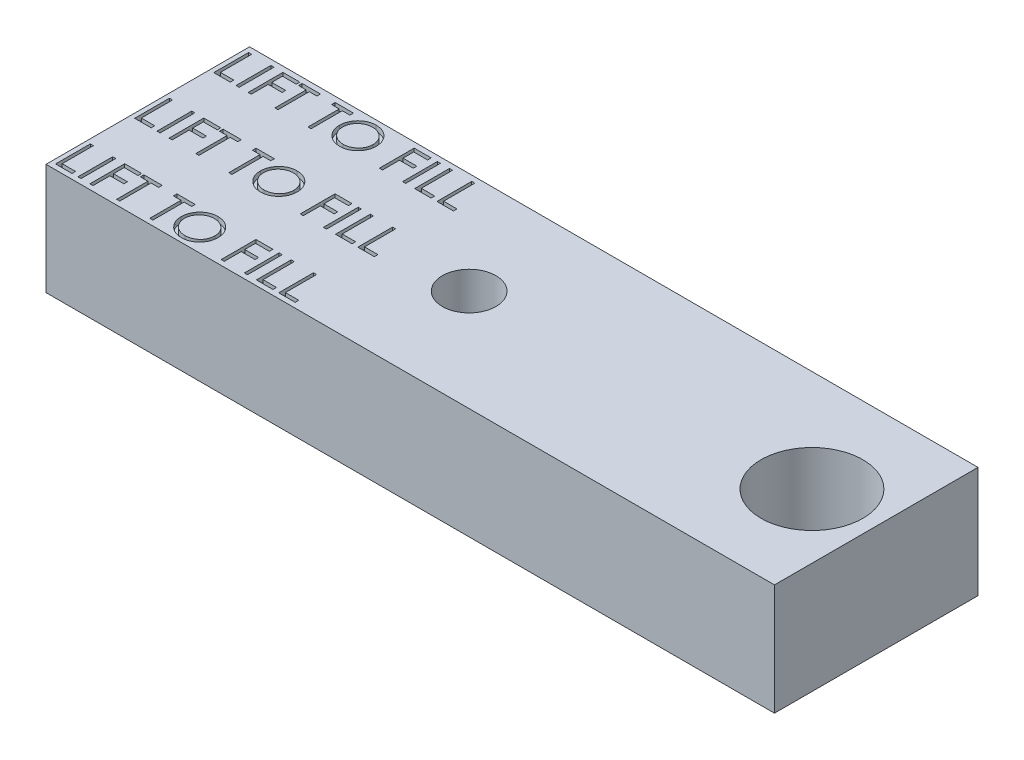
SolidWorks part; units mm, degrees
ref_plane "Front Plane" through (0, 0, 0) normal (0, 0, 1) x (1, 0, 0)
ref_plane "Top Plane" through (0, 0, 0) normal (0, 1, 0) x (1, 0, 0)
ref_plane "Right Plane" through (0, 0, 0) normal (1, 0, 0) x (0, 0, -1)
sketch "Sketch1" plane through (0, 0, 0) normal (0, 1, 0) x (1, 0, 0)
  line L1 (0, 0) -> (34.544, 0)
  line L2 (0, 0) -> (0, 9.652)
  line L3 (0, 9.652) -> (34.544, 9.652)
  line L4 (34.544, 0) -> (34.544, 9.652)
  dimension "D1" = 34.544
  dimension "D2" = 9.652
extrude "Boss-Extrude1" add sketch "Sketch1" along normal blind 5.2705
sketch "Sketch2" plane through (0, 5.2705, 0) normal (0, 1, 0) x (1, 0, 0)
  line L0 (34.544, 0) -> (34.544, 9.652) construction
  line L1 (0, 9.652) -> (0, 0) construction
  line L2 (34.544, 4.826) -> (0, 4.826) construction
  circle A0 centre (31.496, 4.826) radius 2.413
  circle A1 centre (15.24, 4.826) radius 1.27
  dimension "D1" = 4.826
  dimension "D2" = 2.54
  dimension "D3" = 3.048
  dimension "D5" = 15.24
extrude "Cut-Extrude1" cut sketch "Sketch2" against normal through all
sketch "Sketch3" plane through (0, 5.2705, 0) normal (0, 1, 0) x (1, 0, 0)
  line L0 (0, 7.7431) -> (34.544, 7.7431) construction
  line L1 (34.544, 0) -> (34.544, 9.652) construction
  line L2 (0, 9.652) -> (0, 0) construction
  line L4 (0, 0) -> (34.544, 0) construction
  line L5 (0, 9.652) -> (0, 0) construction
  text T0 "LIFT TO FILL\r\nLIFT TO FILL\r\nLIFT TO FILL" font "Century Gothic" height 1.651
extrude "Cut-Extrude2" cut sketch "Sketch3" against normal blind 0.254
